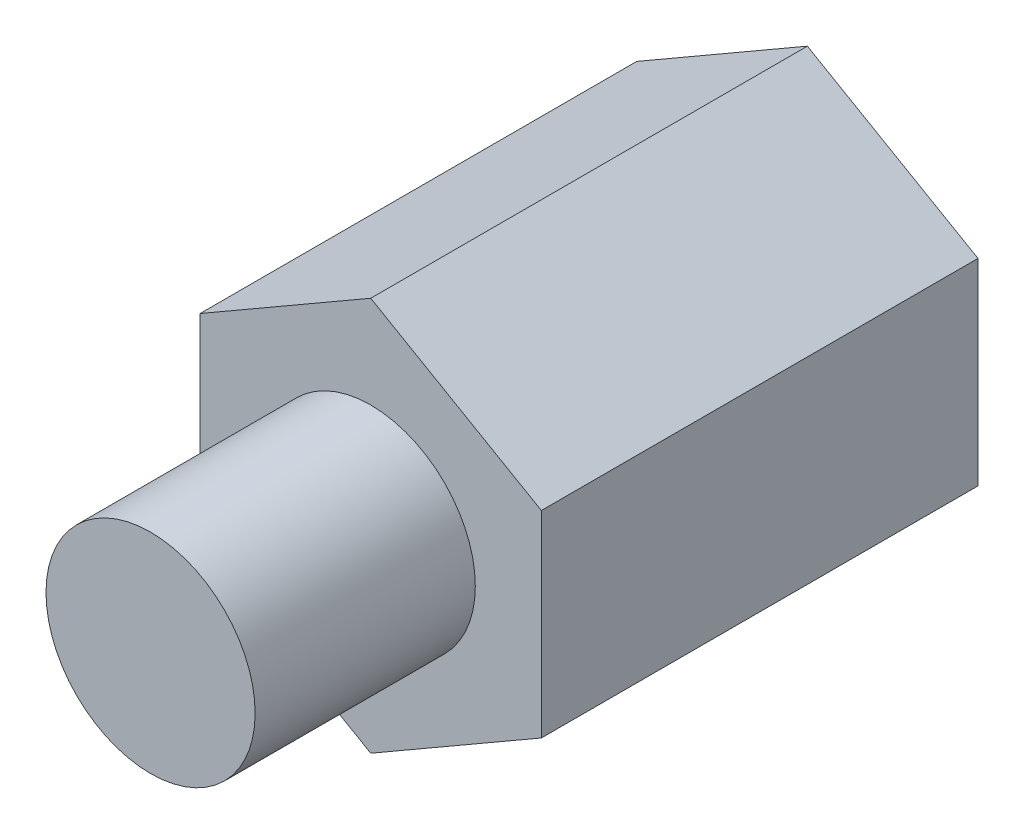
SolidWorks part; units mm, degrees
material "6061-T6 (SS)"
ref_plane "Alzado" through (0, 0, 0) normal (0, 0, 1) x (1, 0, 0)
ref_plane "Planta" through (0, 0, 0) normal (0, 1, 0) x (1, 0, 0)
ref_plane "Vista lateral" through (0, 0, 0) normal (1, 0, 0) x (0, 0, -1)
sketch "Croquis1" plane through (0, 0, 0) normal (0, 0, 1) x (1, 0, 0)
  line L1 (0, -2.6847) -> (2.325, -1.3423)
  line L2 (2.325, -1.3423) -> (2.325, 1.3423)
  line L3 (2.325, 1.3423) -> (0, 2.6847)
  line L4 (0, 2.6847) -> (-2.325, 1.3423)
  line L5 (-2.325, 1.3423) -> (-2.325, -1.3423)
  line L6 (-2.325, -1.3423) -> (0, -2.6847)
  circle A0 centre (0, 0) radius 2.325 construction
  circle A1 centre (0, 0) radius 1.2
  dimension "D2" = 2.4
  dimension "D1" = 4.65
extrude "Saliente-Extruir1" add sketch "Croquis1" along normal blind 5.95
sketch "Croquis2" plane through (0, 0, 5.95) normal (0, 0, 1) x (1, 0, 0)
  circle A0 centre (0, 0) radius 1.425
  dimension "D1" = 2.85
extrude "Saliente-Extruir2" add sketch "Croquis2" along normal blind 3
